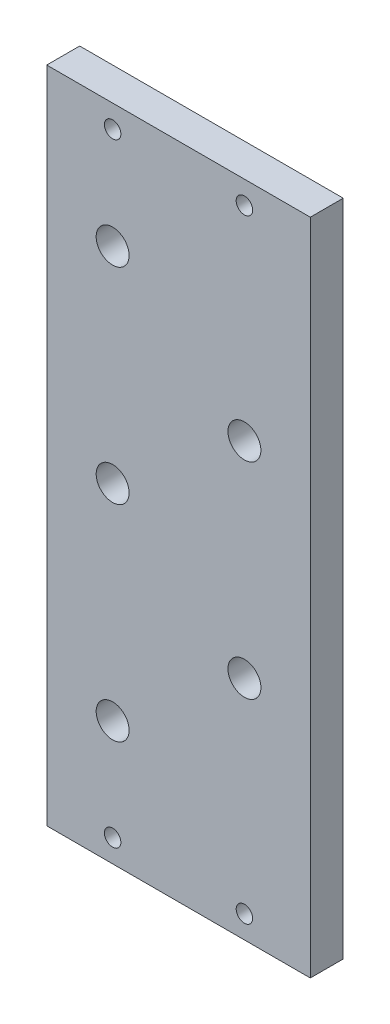
SolidWorks part; units mm, degrees
material "Perspex (TM) GS Acrylic Cast Sheet"
ref_plane "Front Plane" through (0, 0, 0) normal (0, 0, 1) x (1, 0, 0)
ref_plane "Top Plane" through (0, 0, 0) normal (0, 1, 0) x (1, 0, 0)
ref_plane "Right Plane" through (0, 0, 0) normal (1, 0, 0) x (0, 0, -1)
sketch "Sketch1" plane through (0, 0, 0) normal (0, 0, 1) x (1, 0, 0)
  line L1 (0, 0) -> (101.6, 0)
  line L2 (0, 0) -> (0, 254)
  line L3 (0, 254) -> (101.6, 254)
  line L4 (101.6, 0) -> (101.6, 254)
extrude "Boss-Extrude1" add sketch "Sketch1" along normal blind 12.7
sketch "Sketch2" plane through (0, 0, 12.7) normal (0, 0, 1) x (1, 0, 0)
  line L0 (0, 127) -> (101.6, 127) construction
  line L1 (0, 254) -> (0, 0) construction
  line L2 (101.6, 0) -> (101.6, 254) construction
  line L3 (25.4, 241.427) -> (25.4, 12.573) construction
  line L4 (101.6, 254) -> (0, 254) construction
  line L7 (76.2, 254) -> (76.2, 0) construction
  line L8 (0, 0) -> (101.6, 0) construction
  circle A0 centre (25.4, 47.752) radius 6.35
  circle A1 centre (76.2, 87.376) radius 6.35
  circle A2 centre (25.4, 127) radius 6.35
  circle A3 centre (76.2, 166.624) radius 6.35
  circle A4 centre (25.4, 206.248) radius 6.35
  circle A5 centre (25.4, 8.763) radius 3.175
  circle A6 centre (76.2, 8.763) radius 3.175
  circle A7 centre (25.4, 245.237) radius 3.175
  circle A8 centre (76.2, 245.237) radius 3.175
  dimension "D1" = 47.752
  dimension "D2" = 79.248
  dimension "D3" = 38.989
  dimension "D4" = 39.624
  dimension "D6" = 38.989
  dimension "D5" = 47.752
extrude "Cut-Extrude1" cut sketch "Sketch2" against normal through all
